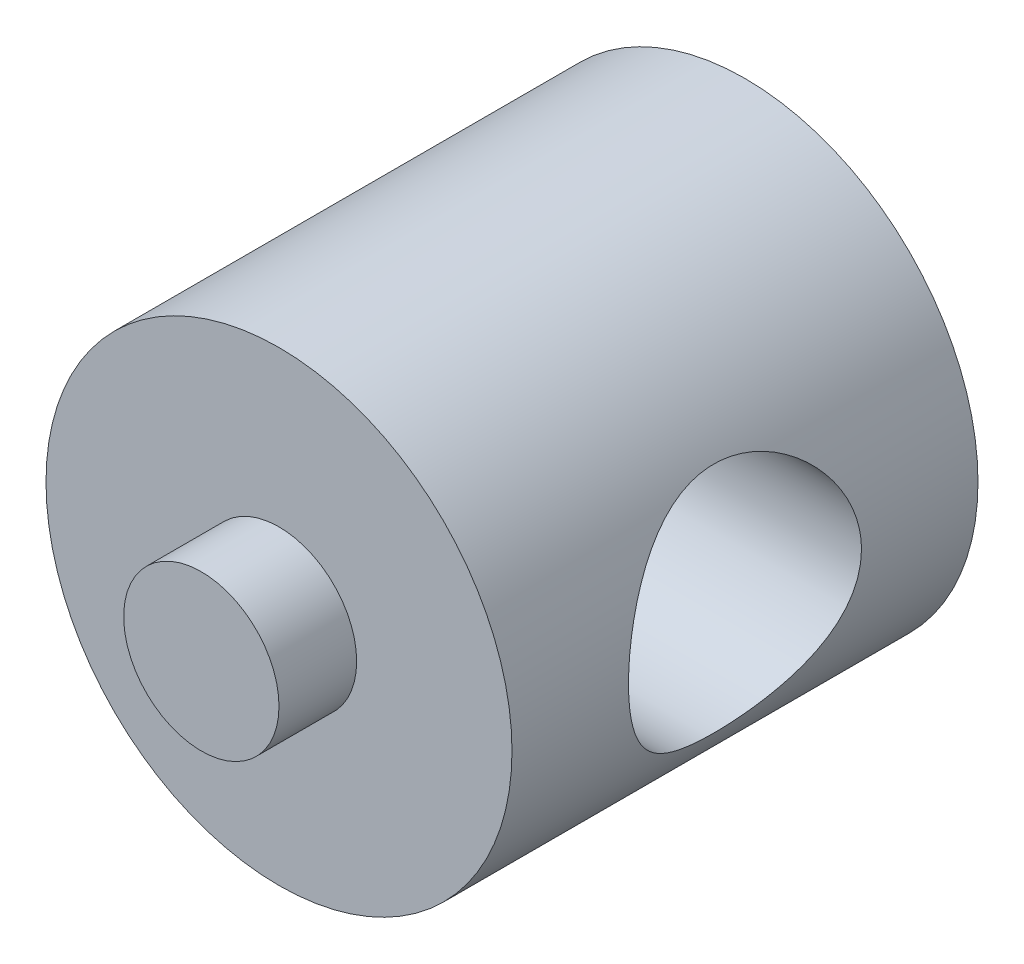
SolidWorks part; units mm, degrees
ref_plane "Front Plane" through (0, 0, 0) normal (0, 0, 1) x (1, 0, 0)
ref_plane "Top Plane" through (0, 0, 0) normal (0, 1, 0) x (1, 0, 0)
ref_plane "Right Plane" through (0, 0, 0) normal (1, 0, 0) x (0, 0, -1)
sketch "Sketch1" plane through (0, 0, 0) normal (0, 0, 1) x (1, 0, 0)
  circle A0 centre (0, 0) radius 9.525
  dimension "D1" = 19.05
extrude "Boss-Extrude1" add sketch "Sketch1" along normal mid plane 19.05
sketch "Sketch2" plane through (0, 0, 0) normal (0, 0, 1) x (1, 0, 0)
  circle A0 centre (0, 0) radius 3.175
  dimension "D1" = 6.35
extrude "Boss-Extrude2" add sketch "Sketch2" along normal mid plane 25.4
sketch "Sketch3" plane through (0, 0, 0) normal (1, 0, 0) x (0, 0, -1)
  circle A0 centre (0, 0) radius 4.7625
  dimension "D1" = 9.525
extrude "Cut-Extrude1" cut sketch "Sketch3" against normal through all both and the other way through all
